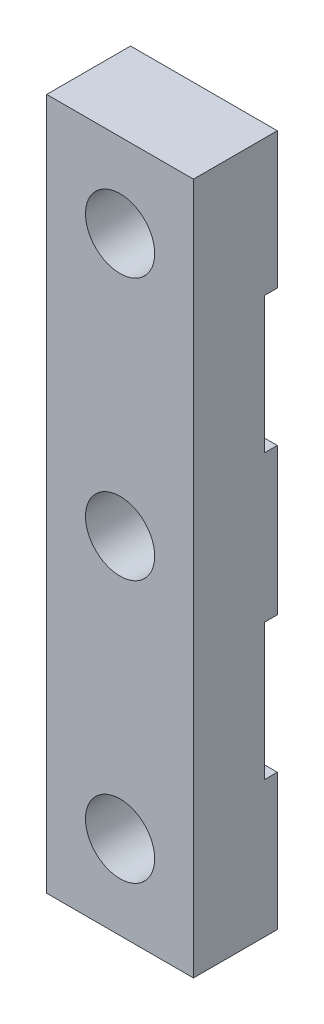
SolidWorks part; units mm, degrees
ref_plane "Plano frontal" through (0, 0, 0) normal (0, 0, 1) x (1, 0, 0)
ref_plane "Plano superior" through (0, 0, 0) normal (0, 1, 0) x (1, 0, 0)
ref_plane "Plano direito" through (0, 0, 0) normal (1, 0, 0) x (0, 0, -1)
sketch "Esboço1" plane through (0, 0, 0) normal (0, 0, 1) x (1, 0, 0)
  line L1 (-3.5, 16.5) -> (3.5, 16.5)
  line L2 (-3.5, 16.5) -> (-3.5, -16.5)
  line L3 (-3.5, -16.5) -> (3.5, -16.5)
  line L4 (3.5, 16.5) -> (3.5, -16.5)
  circle A0 centre (0, 0) radius 1.65
  circle A1 centre (0, 12.5) radius 1.65
  circle A2 centre (0, -12.5) radius 1.65
  point P12 (3.5, 0)
  point P14 (0, -16.5)
  point P20 (0, 16.5)
  dimension "D1" = 3.3
  dimension "D2" = 4
  dimension "D3" = 12.5
  dimension "D4" = 4
  dimension "D5" = 7
extrude "Ressalto-extrusão1" add sketch "Esboço1" along normal blind 4
sketch "Esboço2" plane through (-3.5, 0, 0) normal (-1, 0, 0) x (0, 0, 1)
  line L0 (0, 16.5) -> (0, -16.5) construction
  line L1 (0, 10) -> (0.6, 10)
  line L2 (0, 10) -> (0, 3.5)
  line L3 (0, 3.5) -> (0.6, 3.5)
  line L4 (0.6, 10) -> (0.6, 3.5)
  line L6 (0, -3.5) -> (0.6, -3.5)
  line L7 (0, -3.5) -> (0, -10)
  line L8 (0, -10) -> (0.6, -10)
  line L9 (0.6, -3.5) -> (0.6, -10)
  dimension "D1" = 3.5
  dimension "D2" = 3.5
  dimension "D3" = 6.5
  dimension "D4" = 6.5
  dimension "D5" = 0.6
extrude "Corte-extrusão1" cut sketch "Esboço2" against normal through all
